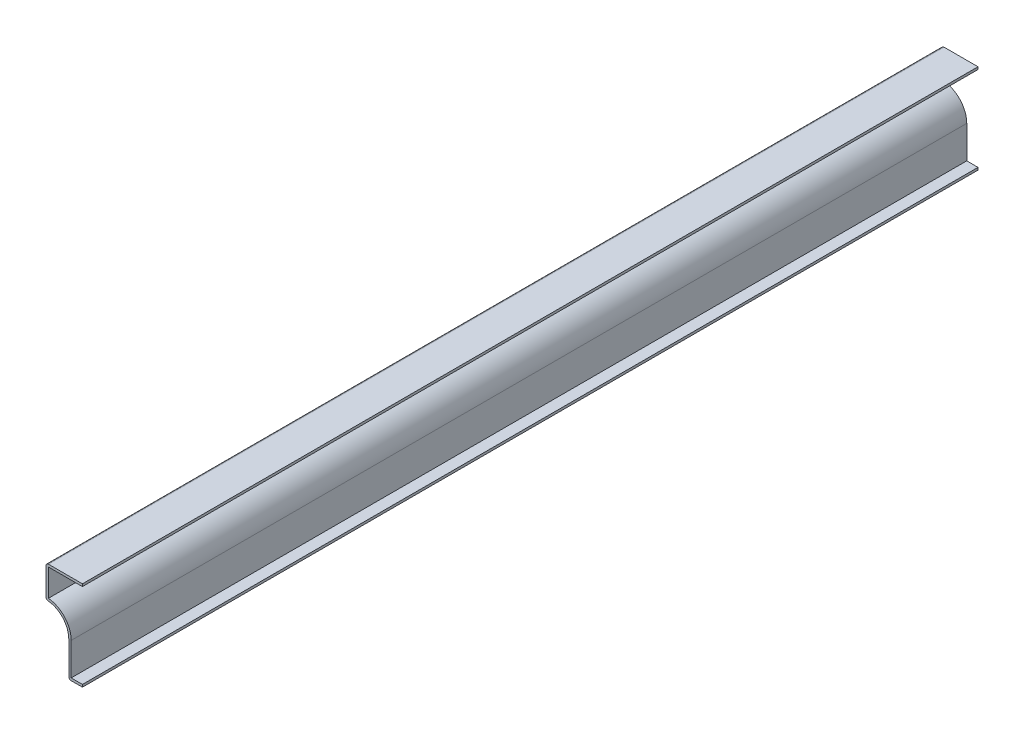
SolidWorks part; units mm, degrees
ref_plane "Front Plane" through (0, 0, 0) normal (0, 0, 1) x (1, 0, 0)
ref_plane "Top Plane" through (0, 0, 0) normal (0, 1, 0) x (1, 0, 0)
ref_plane "Right Plane" through (0, 0, 0) normal (1, 0, 0) x (0, 0, -1)
sketch "Sketch1" plane through (0, 0, 0) normal (0, 0, 1) x (1, 0, 0)
  line L0 (0, 0) -> (0, 46.8312) construction
  line L1 (0, 46.8312) -> (-19.05, 46.8312)
  line L2 (-19.05, 46.8312) -> (-19.05, 30.1625)
  line L3 (-7.1438, 18.2562) -> (-7.1437, 0)
  line L4 (-7.1437, 0) -> (0, 0)
  arc A0 (-19.05, 30.1625) -> (-7.1438, 18.2562) centre (-19.05, 18.2562) cw
  point P8 (0, 0)
  point P9 (-19.8344, 9.1002)
  point P10 (-8.2244, 18.3037)
  point P11 (-16.4491, 46.7365)
  point P12 (-17.7165, 46.8312)
  dimension "D5" = 11.9062
  dimension "D1" = 7.1437
  dimension "D2" = 16.6687
  dimension "D3" = 11.9062
  dimension "D4" = 30.1625
  dimension "D6" = 19.05
  dimension "D7" = 46.8312
extrude "Extrude-Thin1" add sketch "Sketch1" against normal blind 468.3125 thin thin type one direction reverse wall 1.27
fillet "Fillet1" radius 1.27 3 edges at (-7.1437, 0, -234.1562) (-19.05, 30.1625, -234.1562) (-19.05, 46.8312, -234.1562)
